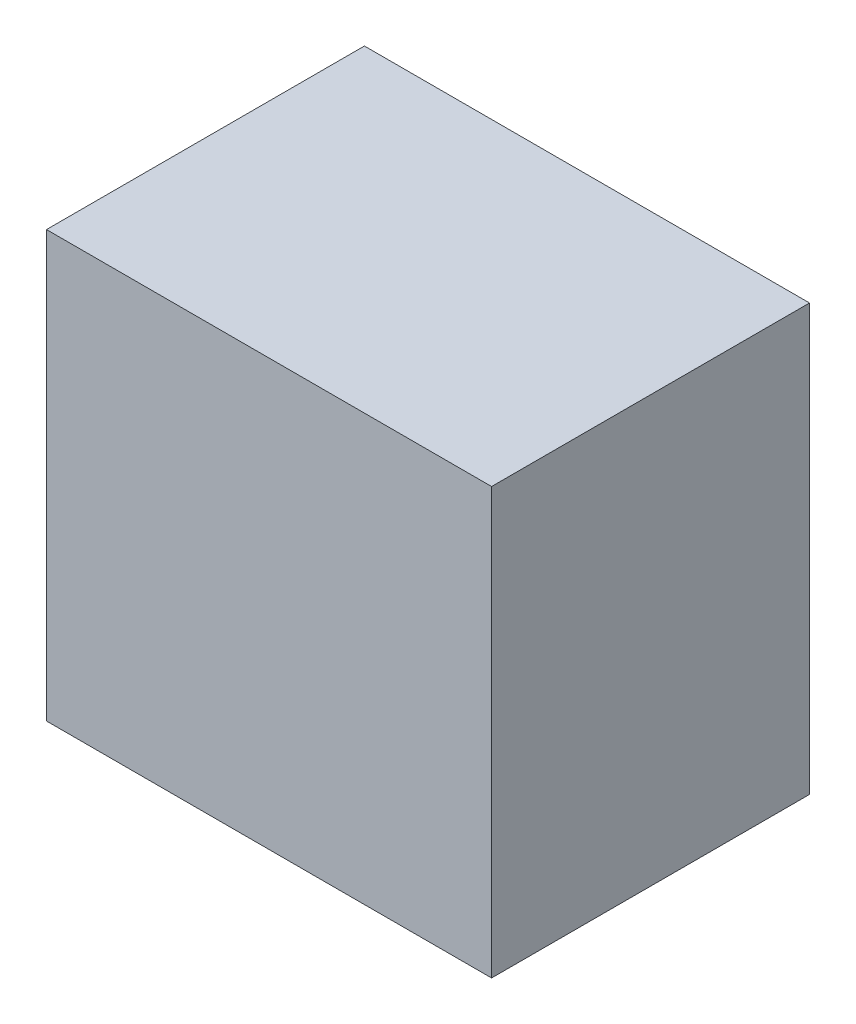
SolidWorks part; units mm, degrees
ref_plane "Front Plane" through (0, 0, 0) normal (0, 0, 1) x (1, 0, 0)
ref_plane "Top Plane" through (0, 0, 0) normal (0, 1, 0) x (1, 0, 0)
ref_plane "Right Plane" through (0, 0, 0) normal (1, 0, 0) x (0, 0, -1)
sketch "Sketch1" plane through (0, 0, 0) normal (0, 0, 1) x (1, 0, 0)
  line L1 (-68.7479, 74.7831) -> (109.0521, 74.7831)
  line L2 (-68.7479, 74.7831) -> (-68.7479, -95.25)
  line L3 (-68.7479, -95.25) -> (109.0521, -95.25)
  line L4 (109.0521, 74.7831) -> (109.0521, -95.25)
  dimension "D1" = 177.8
extrude "Boss-Extrude1" add sketch "Sketch1" along normal blind 127
